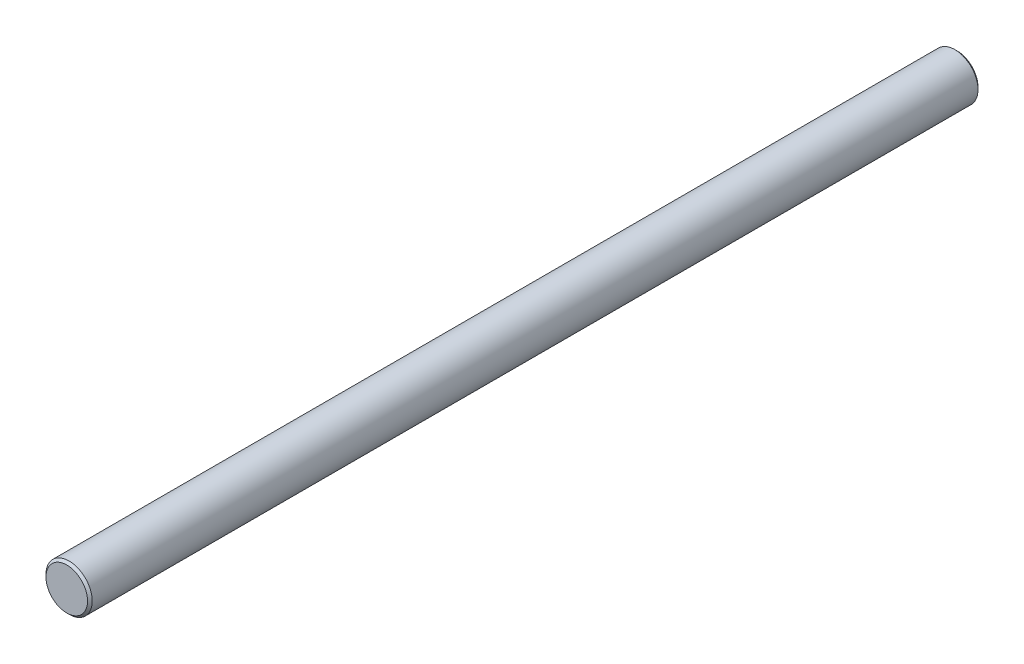
SolidWorks part; units mm, degrees
ref_plane "Front Plane" through (0, 0, 0) normal (0, 0, 1) x (1, 0, 0)
ref_plane "Top Plane" through (0, 0, 0) normal (0, 1, 0) x (1, 0, 0)
ref_plane "Right Plane" through (0, 0, 0) normal (1, 0, 0) x (0, 0, -1)
sketch "Sketch1" plane through (0, 0, 0) normal (0, 0, 1) x (1, 0, 0)
  circle A0 centre (0, 0) radius 10
  dimension "D1" = 20
extrude "Boss-Extrude1" add sketch "Sketch1" along normal blind 385
chamfer "Chamfer1" distance 1 angle 45 2 edges at (10, 0, 0) (10, 0, 385)
